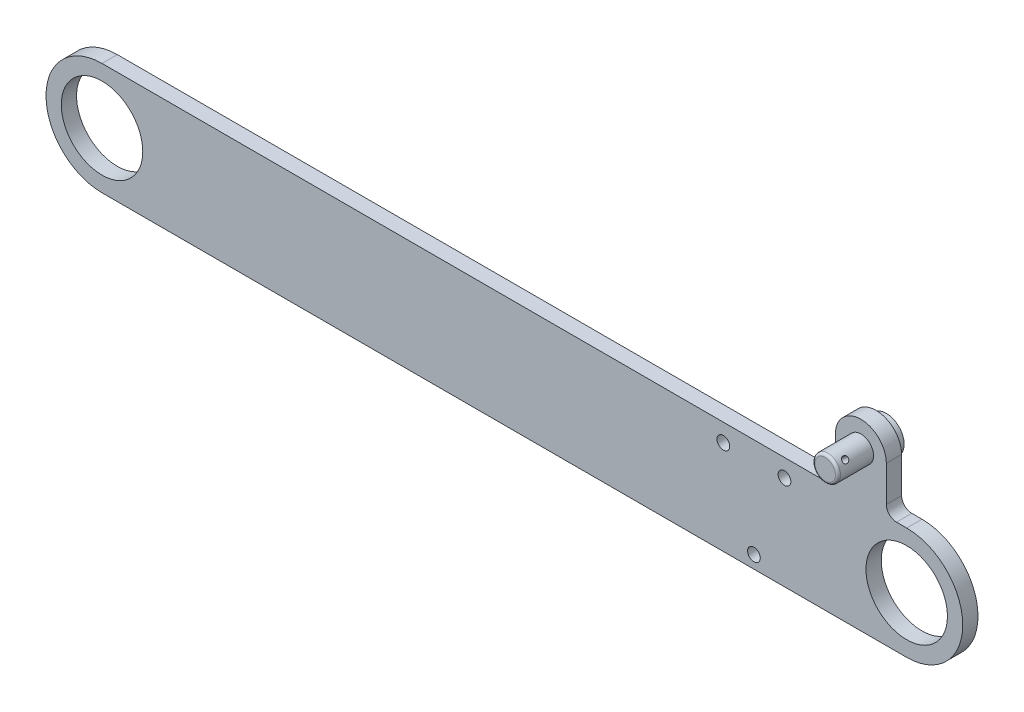
SolidWorks part; units mm, degrees
material "E24"
ref_plane "Face" through (0, 0, 0) normal (0, 0, 1) x (1, 0, 0)
ref_plane "Dessus" through (0, 0, 0) normal (0, 1, 0) x (1, 0, 0)
ref_plane "Droite" through (0, 0, 0) normal (1, 0, 0) x (0, 0, -1)
sketch "Esquisse1" plane through (0, 0, 0) normal (0, 0, 1) x (1, 0, 0)
  line L1 (79, 11) -> (-79, 11)
  line L3 (79, -11) -> (-79, -11)
  line L5 (79, 11) -> (-79, -11) construction
  line L6 (79, -11) -> (-79, 11) construction
  arc A0 (-79, 11) -> (-79, -11) centre (-79, 0) ccw
  arc A1 (79, -11) -> (79, 11) centre (79, 0) ccw
  circle A2 centre (-79, 0) radius 8
  circle A3 centre (79, 0) radius 8
  point P0 (0, 0)
  dimension "D1" = 16
  dimension "D3" = 158
  dimension "D2" = 3
extrude "Boss.-Extru.1" add sketch "Esquisse1" along normal blind 3
sketch "Esquisse2" plane through (0, 0, 3) normal (0, 0, 1) x (1, 0, 0)
  line L0 (75, 11) -> (75, 20)
  line L1 (79, 11) -> (-79, 11) construction
  line L2 (65, 20) -> (65, 11)
  line L3 (65, 11) -> (75, 11)
  arc A0 (75, 20) -> (65, 20) centre (70, 20) ccw
  arc A1 (79, -11) -> (79, 11) centre (79, 0) ccw construction
  circle A2 centre (70, 20) radius 2.5
  point P6 (90, 0)
  dimension "D4" = 5
  dimension "D1" = 10
  dimension "D2" = 9
  dimension "D3" = 15
extrude "Boss.-Extru.2" add sketch "Esquisse2" against normal up to surface (3 mm away) up to face at (0, 0, 0)
fillet "Congé2" radius 2 2 edges at (65, 11, 1.5) (75, 11, 1.5)
sketch "Esquisse3" plane through (0, 0, 0) normal (0, 0, -1) x (-1, 0, 0)
  circle A0 centre (-70, 20) radius 3.5
  dimension "D1" = 7
extrude "Boss.-Extru.3" add sketch "Esquisse3" along normal blind 2 separate body
sketch "Esquisse4" plane through (0, 0, 0) normal (0, 0, 1) x (1, 0, 0)
  circle A0 centre (70, 20) radius 2.5 construction
  circle A1 centre (70, 20) radius 2.5
extrude "Boss.-Extru.4" add sketch "Esquisse4" along normal blind 10 separate body
fillet "Congé3" radius 0.5 1 edges at (72.5, 20, 10)
hole_wizard "Diamètre du perçage Ø1.2 (1.2)1" positions "Esquisse3D1" profile "Esquisse5" hole size "Ø1.2" standard "ISO" end condition through all
sketch3d "Esquisse3D1"
  line L2 (71.9321, 21.5865, 8) -> (71.9321, 21.5865, 9.5) construction
  circle A1 centre (70, 20, 9.5) radius 2.5 construction
  point P0 (71.9321, 21.5865, 8)
  point P13 (70, 20, 7)
  dimension "D1" = 1.5
sketch "Esquisse5" plane through (71.9321, 21.5865, 8) normal (0, 0, 1) x (-0.6346, 0.7728, 0)
  line L0 (0, 0) -> (0, 145.8252)
  line L1 (0, 145.8252) -> (0.6, 145.8252)
  line L2 (0.6, 145.8252) -> (0.6, 0)
  line L5 (0.6, 0) -> (0, 0)
  line L11 (0, -6.35) -> (0, 107.95) construction
  dimension "Diamètre du perçage jusqu'au prochain" = 1.2
  dimension "Profondeur du perçage jusqu'au prochain" = 145.8252
sketch "Esquisse6" plane through (0, 0, 0) normal (0, 0, -1) x (-1, 0, 0)
  circle A0 centre (-55, 7.5) radius 1.25
  circle A1 centre (-43, 7.5) radius 1.25
  circle A2 centre (-49, -8.5) radius 1.25
  dimension "D1" = 2.5
extrude "Enlèv. mat.-Extru.1" cut sketch "Esquisse6" against normal through all
